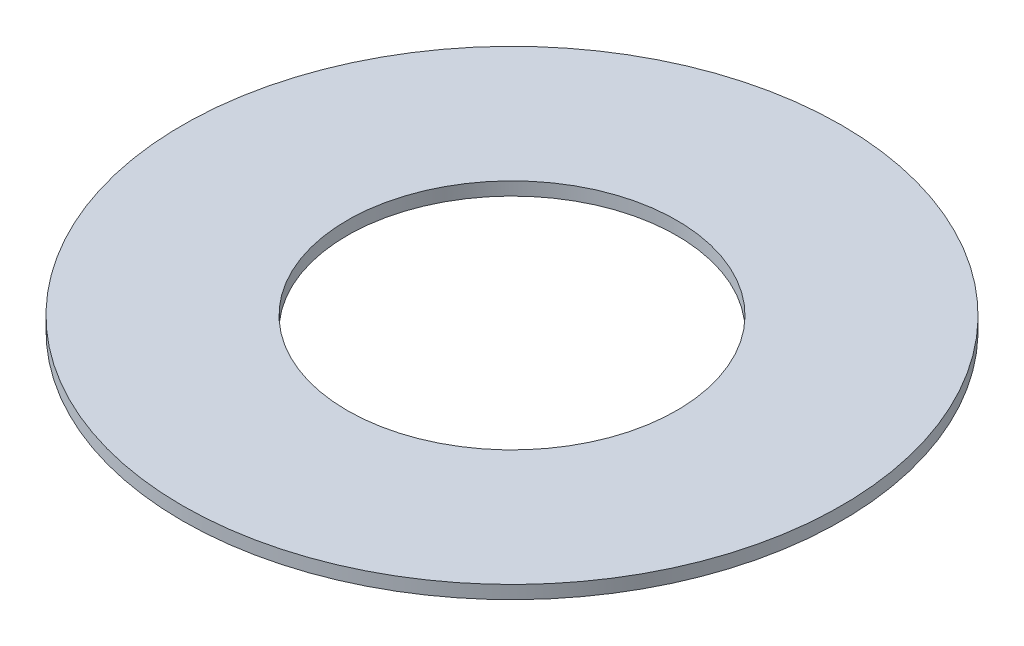
SolidWorks part; units mm, degrees
ref_plane "Front Plane" through (0, 0, 0) normal (0, 0, 1) x (1, 0, 0)
ref_plane "Top Plane" through (0, 0, 0) normal (0, 1, 0) x (1, 0, 0)
ref_plane "Right Plane" through (0, 0, 0) normal (1, 0, 0) x (0, 0, -1)
sketch "Sketch1" plane through (0, 0, 0) normal (0, 1, 0) x (1, 0, 0)
  circle A0 centre (0, 0) radius 5
  dimension "OD" = 10
extrude "Boss-Extrude1" add sketch "Sketch1" along normal blind 0.2
sketch "Sketch5" plane through (0, 0.2, 0) normal (0, 1, 0) x (-1, 0, 0)
  circle A0 centre (0, 0) radius 2.5
  dimension "ID" = 5
extrude "Cut-Extrude1" cut sketch "Sketch5" against normal through all
